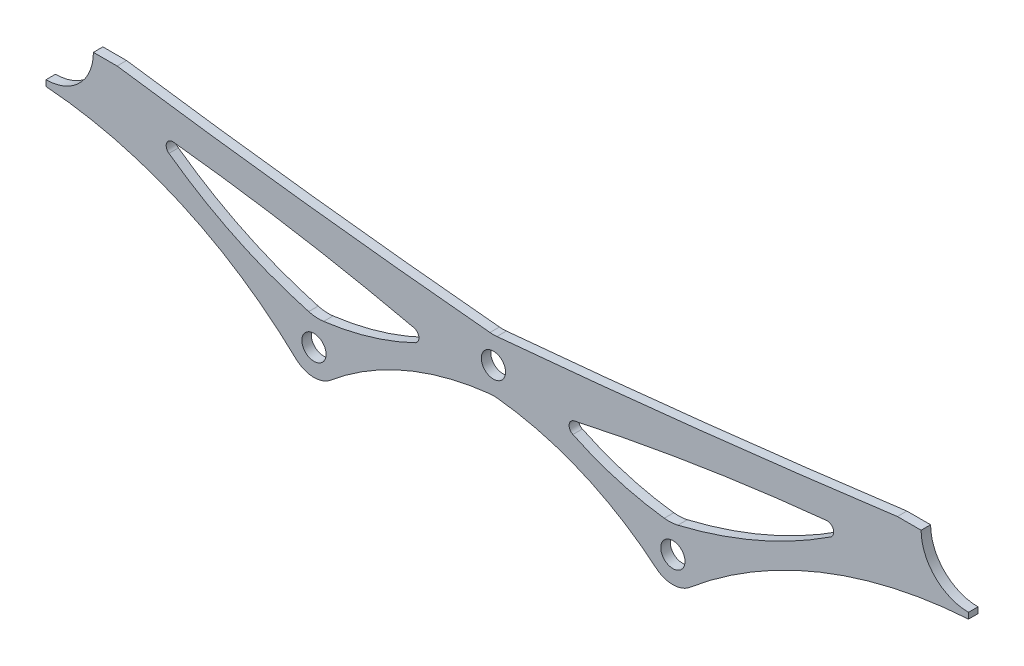
SolidWorks part; units mm, degrees
material "AISI 4130 Steel, normalized at 870C"
ref_plane "Front" through (0, 0, 0) normal (0, 0, 1) x (1, 0, 0)
ref_plane "Top" through (0, 0, 0) normal (0, 1, 0) x (1, 0, 0)
ref_plane "Right" through (0, 0, 0) normal (1, 0, 0) x (0, 0, -1)
sketch "Sketch1207" plane through (0, 0, 0) normal (0, 0, 1) x (1, 0, 0)
  line L0 (-1533.5947, 259.715) -> (-1533.5947, 308.9142) construction
  line L1 (-1653.472, 346.71) -> (-1533.5951, 327.715) construction
  line L3 (-1653.472, 346.71) -> (-1581.678, 307.7983) construction
  line L4 (-1581.678, 307.7983) -> (-1533.5951, 327.715) construction
  line L5 (-1533.5951, 327.715) -> (-1485.5115, 307.7983) construction
  line L6 (-1485.5115, 307.7983) -> (-1406.301, 346.71) construction
  line L7 (-1406.301, 346.71) -> (-1459.0421, 330.258) construction
  line L8 (-1592.9075, 341.1637) -> (-1594.1596, 333.2613) construction
  line L9 (-1617.8505, 307.7983) -> (-1449.0407, 307.7983) construction
  line L10 (-1428.8331, 343.3477) -> (-1426.7486, 336.6652) construction
  line L11 (-1654.9015, 344.0725) -> (-1595.9534, 312.1231) construction
  line L12 (-1438.8187, 344.9765) -> (-1437.6195, 336.9405) construction
  line L13 (-1653.472, 346.71) -> (-1617.7488, 334.5971) construction
  line L14 (-1581.678, 307.7983) -> (-1585.2135, 311.3338) construction
  line L15 (-1510.7013, 314.985) -> (-1508.4052, 320.5283) construction
  line L16 (-1629.4272, 342.9) -> (-1632.0688, 335.1096) construction
  line L17 (-1556.4885, 314.985) -> (-1558.7846, 320.5283) construction
  line L18 (-1472.4093, 310.8922) -> (-1404.9782, 344.0174) construction
  line L19 (-1474.5247, 316.5379) -> (-1407.6237, 349.4026) construction
  line L21 (-1470.5384, 341.1692) -> (-1469.3576, 333.2558) construction
  line L22 (-1624.3138, 345.2792) -> (-1625.5854, 337.2543) construction
  line L23 (-1484.1887, 305.1056) -> (-1404.9782, 344.0174) construction
  line L26 (-1486.8342, 310.4909) -> (-1407.6237, 349.4026) construction
  line L27 (-1533.5951, 327.715) -> (-1406.301, 346.71) construction
  line L29 (-1581.678, 307.7983) -> (-1577.7889, 303.9092) construction
  line L30 (-1652.0425, 349.3475) -> (-1590.8934, 316.2052) construction
  line L31 (-1652.0425, 349.3475) -> (-1580.2485, 310.4358) construction
  line L32 (-1654.9015, 344.0725) -> (-1583.1075, 305.1607) construction
  line L34 (-1653.472, 332.4225) -> (-1653.472, 334.01)
  line L35 (-1640.772, 346.71) -> (-1634.422, 346.71)
  line L36 (-1425.351, 346.71) -> (-1419.001, 346.71)
  line L37 (-1406.301, 334.01) -> (-1406.301, 332.4225)
  line L53 (-1653.472, 346.71) -> (-1406.301, 346.71) construction
  circle A0 centre (-1533.5947, 259.715) radius 62.5 construction
  arc A1 (-1634.422, 346.71) -> (-1532.9466, 334.6849) centre (-1344.9459, 2355.3209) ccw
  circle A2 centre (-1533.5947, 259.715) radius 73 construction
  circle A3 centre (-1533.5951, 327.715) radius 3.25 construction
  circle A4 centre (-1485.5115, 307.7983) radius 3.25 construction
  arc A6 (-1586.5005, 302.7245) -> (-1577.1806, 302.4342) centre (-1581.678, 307.7983) ccw
  arc A7 (-1490.0089, 302.4342) -> (-1481.0008, 302.4453) centre (-1485.5115, 307.7983) ccw
  arc A8 (-1625.5854, 337.2543) -> (-1550.2518, 324.6742) centre (-1682.0132, -232.5043) cw
  circle A10 centre (-1581.678, 307.7983) radius 3.25 construction
  circle A11 centre (-1533.5951, 327.715) radius 7 construction
  circle A12 centre (-1485.5115, 307.7983) radius 7 construction
  arc A14 (-1581.1383, 314.8811) -> (-1550.2518, 324.6742) centre (-1589.2636, 394.1107) ccw
  arc A16 (-1437.6195, 336.9405) -> (-1516.7168, 324.5503) centre (-1383.7352, -265.7181) ccw
  circle A18 centre (-1581.678, 307.7983) radius 7 construction
  circle A19 centre (-1533.5947, 259.715) radius 57 construction
  circle A20 centre (-1406.301, 346.71) radius 12.7 construction
  circle A21 centre (-1653.472, 346.71) radius 14.2875 construction
  circle A22 centre (-1406.301, 346.71) radius 14.2875 construction
  arc A23 (-1653.472, 332.4225) -> (-1586.5005, 302.7245) centre (-1661.6163, 223.6942) cw
  circle A24 centre (-1653.472, 346.71) radius 12.7 construction
  arc A25 (-1580.0009, 314.5944) -> (-1625.5854, 337.2543) centre (-1551.9787, 428.1468) cw
  circle A26 centre (-1581.678, 307.7983) radius 3.25
  circle A27 centre (-1533.5951, 327.715) radius 3.25
  circle A28 centre (-1485.5115, 307.7983) radius 3.25
  arc A29 (-1625.5854, 337.2543) -> (-1535.3877, 320.9484) centre (-1682.0132, -232.5041) cw construction
  circle A30 centre (-1406.301, 346.71) radius 19.05 construction
  arc A31 (-1534.2202, 334.687) -> (-1425.351, 346.71) centre (-1772.0078, 2986.7973) ccw
  arc A32 (-1531.8812, 320.928) -> (-1437.6195, 336.9405) centre (-1383.7352, -265.7181) cw construction
  arc A33 (-1534.2079, 320.7419) -> (-1490.0089, 302.4342) centre (-1541.1807, 241.4006) cw
  arc A34 (-1582.2908, 314.7714) -> (-1538.0925, 333.079) centre (-1589.2636, 394.1107) ccw construction
  arc A35 (-1577.1806, 302.4342) -> (-1532.9822, 320.7419) centre (-1526.0094, 241.4025) cw
  arc A36 (-1529.0977, 333.0791) -> (-1484.8987, 314.7714) centre (-1477.9258, 394.1127) ccw construction
  arc A37 (-1487.0015, 314.6378) -> (-1437.6195, 336.9405) centre (-1514.7039, 441.797) ccw
  circle A38 centre (-1653.472, 346.71) radius 19.05 construction
  arc A39 (-1481.0008, 302.4453) -> (-1406.301, 332.4225) centre (-1398.2066, 204.1916) cw
  arc A40 (-1653.472, 334.01) -> (-1640.772, 346.71) centre (-1653.472, 346.71) ccw
  arc A41 (-1419.001, 346.71) -> (-1406.301, 334.01) centre (-1406.301, 346.71) ccw
  arc A42 (-1516.7168, 324.5503) -> (-1485.952, 314.871) centre (-1477.9258, 394.1127) ccw
  point P6 (-1469.948, 337.2125)
  point P64 (-1427.7908, 340.0065)
  point P72 (-1509.5533, 317.7566)
  point P73 (-1557.6365, 317.7566)
  point P77 (-1593.5335, 337.2125)
  point P92 (-1630.748, 339.0048)
  point P116 (-1624.8068, 342.1679)
  point P120 (-1653.472, 346.71)
  dimension "D3" = 146
  dimension "D4" = 28.575
  dimension "D5" = 125
  dimension "D6" = 6.5
  dimension "D8" = 14
  dimension "D10" = 114
  dimension "D16" = 3
  dimension "D19" = 71.794
  dimension "D20" = 38.9117
  dimension "D21" = 119.877
  dimension "D22" = 18.995
  dimension "D7" = 3
  dimension "D9" = 38.1
  dimension "D11" = 8.001
  dimension "D14" = 25.4
  dimension "D15" = 8.125
  dimension "D26" = 6.5
  dimension "D2" = 119.8773
  dimension "D12" = 3
  dimension "D13" = 6
  dimension "D18" = 86.995
  dimension "D23" = 167.9605
  dimension "D24" = 38.9117
  dimension "D25" = 247.171
  dimension "D17" = 3
extrude "Planetary Inner Tab" add sketch "Sketch1207" against normal blind 2.54 from offset 12.7 separate body offset against normal yes
fillet "Smal Angle Fillet" radius 1.778 4 edges at (-1437.6195, 336.9405, -13.97) (-1516.7168, 324.5503, -13.97) (-1550.2518, 324.6742, -13.97) (-1625.5854, 337.2543, -13.97)
fillet "Large Angle Fillet" radius 10.16 4 edges at (-1533.5831, 334.7442, -13.97) (-1533.5951, 320.6856, -13.97) (-1485.952, 314.871, -13.97) (-1581.1383, 314.8811, -13.97)
equation "\"Firewall main-side offset\"= \"#8 Diameter\" + \"Firewall hole offset\" + \"Firewall arc offset\""
